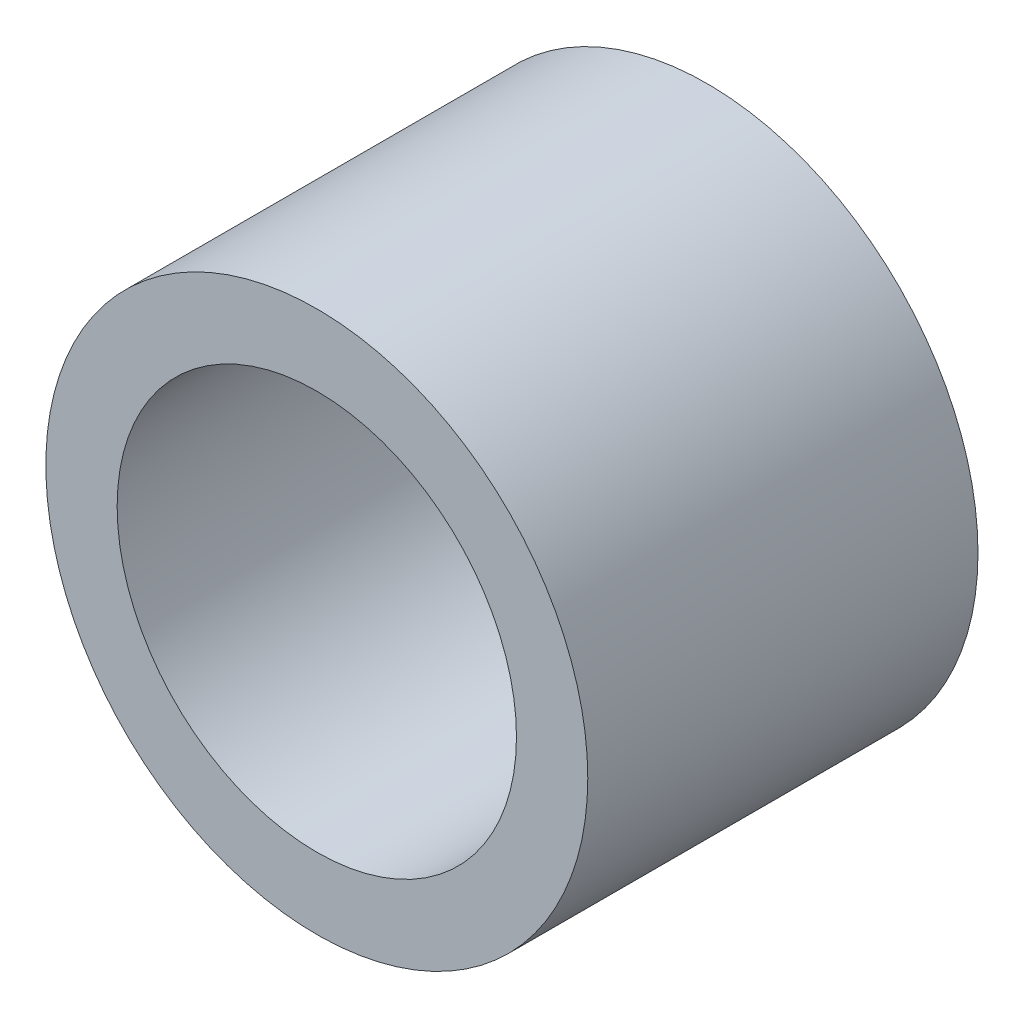
SolidWorks part; units mm, degrees
ref_plane "Front Plane" through (0, 0, 0) normal (0, 0, 1) x (1, 0, 0)
ref_plane "Top Plane" through (0, 0, 0) normal (0, 1, 0) x (1, 0, 0)
ref_plane "Right Plane" through (0, 0, 0) normal (1, 0, 0) x (0, 0, -1)
sketch "Sketch1" plane through (0, 0, 0) normal (0, 0, 1) x (1, 0, 0)
  circle A0 centre (0, 0) radius 4.826
  circle A1 centre (0, 0) radius 3.556
  dimension "D1" = 7.112
  dimension "D2" = 1.27
extrude "Boss-Extrude1" add sketch "Sketch1" along normal blind 6.9494
